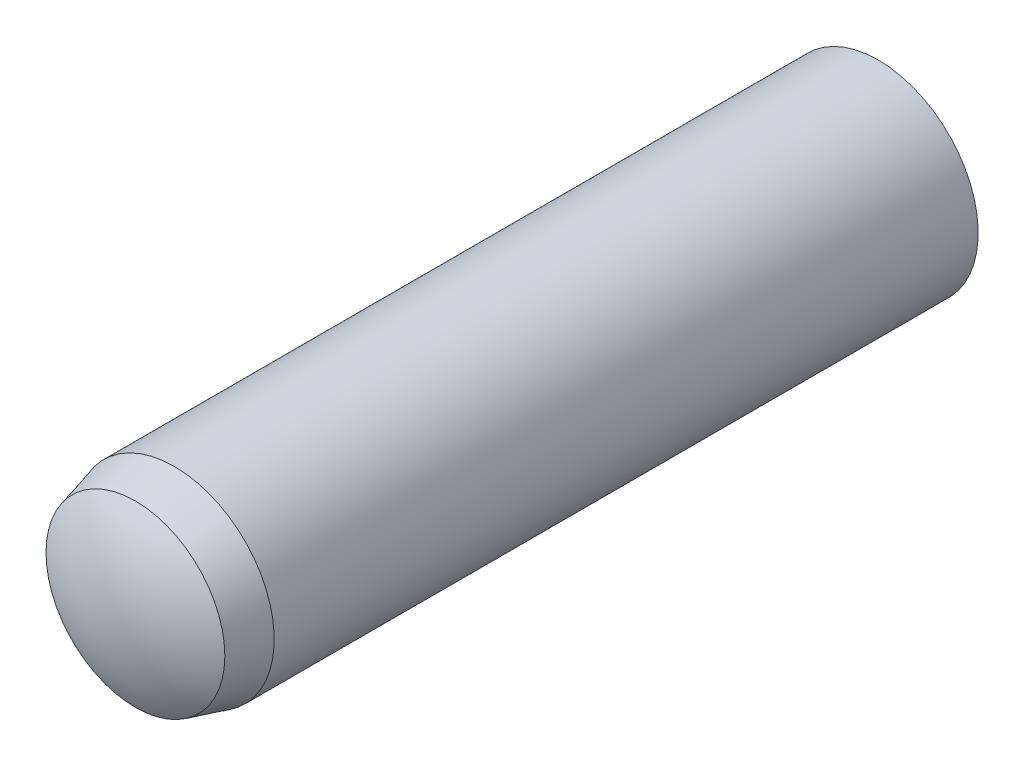
SolidWorks part; units mm, degrees
ref_plane "Front Plane" through (0, 0, 0) normal (0, 0, 1) x (1, 0, 0)
ref_plane "Top Plane" through (0, 0, 0) normal (0, 1, 0) x (1, 0, 0)
ref_plane "Right Plane" through (0, 0, 0) normal (1, 0, 0) x (0, 0, -1)
sketch "Sketch1" plane through (0, 0, 0) normal (0, 0, 1) x (1, 0, 0)
  circle A0 centre (0, 0) radius 1.5
  point P3 (0, 1.5)
  dimension "Diameter" = 3
sketch "Sketch2" plane through (0, 0, 0) normal (1, 0, 0) x (0, 0, -1)
  line L0 (-6, 0) -> (6, 0) construction
  line L1 (-6, 0) -> (-6, 1.5) construction
  line L2 (-6, 1.5) -> (6, 1.5)
  line L3 (6, 1.5) -> (6, 0) construction
  line L4 (-5.61, 1.3432) -> (-5.025, 1.5)
  arc A0 (-6, 0) -> (-5.61, 1.3432) centre (-3.4918, 0) cw
  arc A1 (6, 0) -> (5.55, 1.5) centre (3.275, 0) ccw
  point P2 (0, 0)
  point P11 (-3, 0)
  point P13 (3, 0)
  dimension "Length" = 12
  dimension "D1" = 15
  dimension "D2" = 0.45
  dimension "D3" = 0.975
  dimension "D4" = 0.585
  dimension "D5" = 3
  dimension "D6" = 3
sketch "Sketch3" plane through (0, 0, 0) normal (1, 0, 0) x (0, 0, -1)
  line L0 (-6, 0) -> (6, 0) construction
  line L1 (-5.61, 1.3432) -> (-5.025, 1.5) construction
  line L2 (-6, 0) -> (6, 0)
  line L3 (-5.61, 1.3432) -> (-5.025, 1.5)
  line L4 (-5.025, 1.5) -> (5.55, 1.5)
  arc A0 (6, 0) -> (5.55, 1.5) centre (3.275, 0) ccw construction
  arc A1 (-5.61, 1.3432) -> (-6, 0) centre (-3.4918, 0) ccw construction
  arc A2 (6, 0) -> (5.55, 1.5) centre (3.275, 0) ccw
  arc A3 (-5.61, 1.3432) -> (-6, 0) centre (-3.4918, 0) ccw
revolve "Revolve1" add sketch "Sketch3" angle 360 about L2
equation "\"D2@Sketch2\" = \"Diameter@Sketch1\" * .15"
equation "\"D3@Sketch2\" = \"Diameter@Sketch1\" * .325"
equation "\"D4@Sketch2\" = \"D3@Sketch2\" * .6"
equation "\"D5@Sketch2\"=\"Diameter@Sketch1\""
equation "\"D6@Sketch2\"=\"D5@sketch2\""
